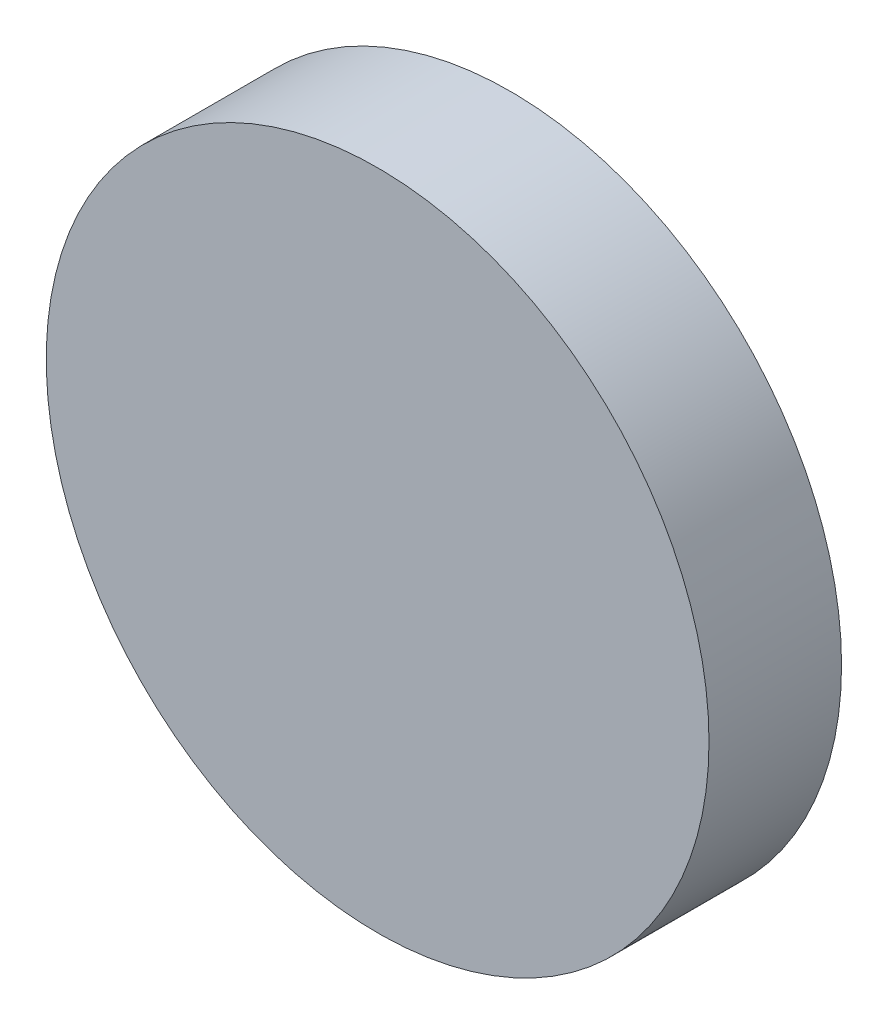
SolidWorks part; units mm, degrees
ref_plane "Front Plane" through (0, 0, 0) normal (0, 0, 1) x (1, 0, 0)
ref_plane "Top Plane" through (0, 0, 0) normal (0, 1, 0) x (1, 0, 0)
ref_plane "Right Plane" through (0, 0, 0) normal (1, 0, 0) x (0, 0, -1)
sketch "Sketch1" plane through (0, 0, 0) normal (0, 0, 1) x (1, 0, 0)
  circle A0 centre (0, 0) radius 250
  dimension "D1" = 500
extrude "Boss-Extrude1" add sketch "Sketch1" along normal blind 100 contours A0
